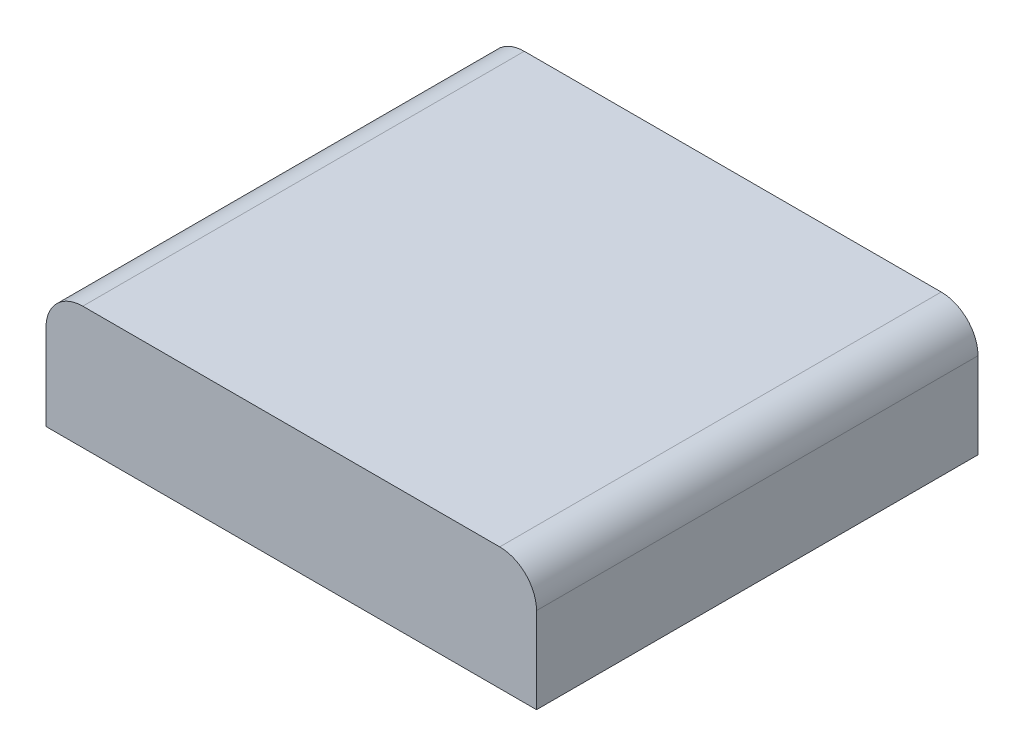
SolidWorks part; units mm, degrees
material "CA"
ref_plane "Front Plane" through (0, 0, 0) normal (0, 0, 1) x (1, 0, 0)
ref_plane "Top Plane" through (0, 0, 0) normal (0, 1, 0) x (1, 0, 0)
ref_plane "Right Plane" through (0, 0, 0) normal (1, 0, 0) x (0, 0, -1)
sketch "Sketch1" plane through (0, 0, 0) normal (0, 0, 1) x (1, 0, 0)
  line L1 (0, 0) -> (63.5, 0)
  line L2 (0, 0) -> (0, 11.1125)
  line L3 (4.7625, 15.875) -> (58.7375, 15.875)
  line L4 (63.5, 0) -> (63.5, 11.1125)
  arc A0 (63.5, 11.1125) -> (58.7375, 15.875) centre (58.7375, 11.1125) ccw
  arc A1 (0, 11.1125) -> (4.7625, 15.875) centre (4.7625, 11.1125) cw
  point P7 (63.5, 15.875)
  point P10 (0, 15.875)
  dimension "D3" = 4.7625
  dimension "D4" = 4.7625
  dimension "D1" = 63.5
  dimension "D2" = 15.875
extrude "Boss-Extrude1" add sketch "Sketch1" along normal blind 57.15
